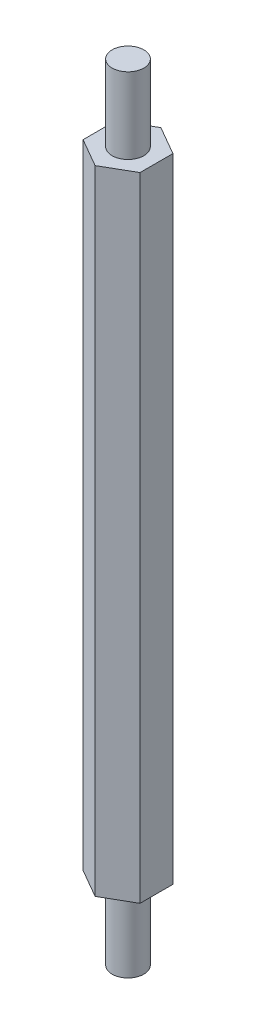
SolidWorks part; units mm, degrees
ref_plane "前视基准面" through (0, 0, 0) normal (0, 0, 1) x (1, 0, 0)
ref_plane "上视基准面" through (0, 0, 0) normal (0, 1, 0) x (1, 0, 0)
ref_plane "右视基准面" through (0, 0, 0) normal (1, 0, 0) x (0, 0, -1)
sketch "草图1" plane through (0, 0, 0) normal (0, 1, 0) x (1, 0, 0)
  line L1 (2.25, -1.299) -> (2.25, 1.299)
  line L2 (2.25, 1.299) -> (0, 2.5981)
  line L3 (0, 2.5981) -> (-2.25, 1.299)
  line L4 (-2.25, 1.299) -> (-2.25, -1.299)
  line L5 (-2.25, -1.299) -> (0, -2.5981)
  line L6 (0, -2.5981) -> (2.25, -1.299)
  circle A0 centre (0, 0) radius 2.25 construction
  point P1 (0, -2.5981)
  dimension "D1" = 4.5
extrude "凸台-拉伸1" add sketch "草图1" along normal mid plane 50
sketch "草图2" plane through (0, 0, 0) normal (0, 1, 0) x (1, 0, 0)
  circle A0 centre (0, 0) radius 1.25
  dimension "D1" = 2.5
extrude "凸台-拉伸2" add sketch "草图2" along normal mid plane 62
